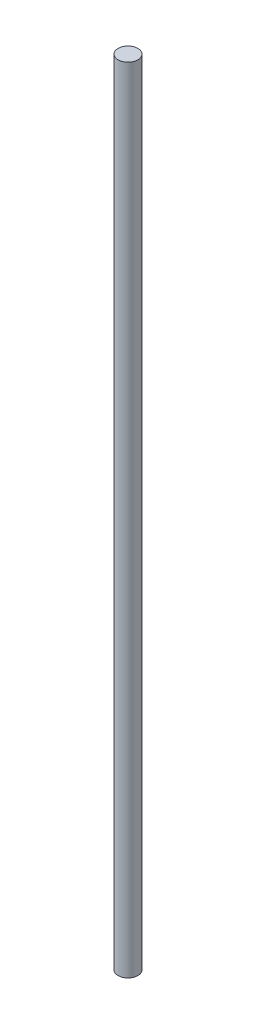
SolidWorks part; units mm, degrees
ref_plane "Front Plane" through (0, 0, 0) normal (0, 0, 1) x (1, 0, 0)
ref_plane "Top Plane" through (0, 0, 0) normal (0, 1, 0) x (1, 0, 0)
ref_plane "Right Plane" through (0, 0, 0) normal (1, 0, 0) x (0, 0, -1)
sketch "Sketch1" plane through (0, 0, 0) normal (0, 1, 0) x (1, 0, 0)
  circle A0 centre (0, 0) radius 1.5875
  dimension "D1" = 3.175
extrude "Boss-Extrude1" add sketch "Sketch1" along normal blind 127
